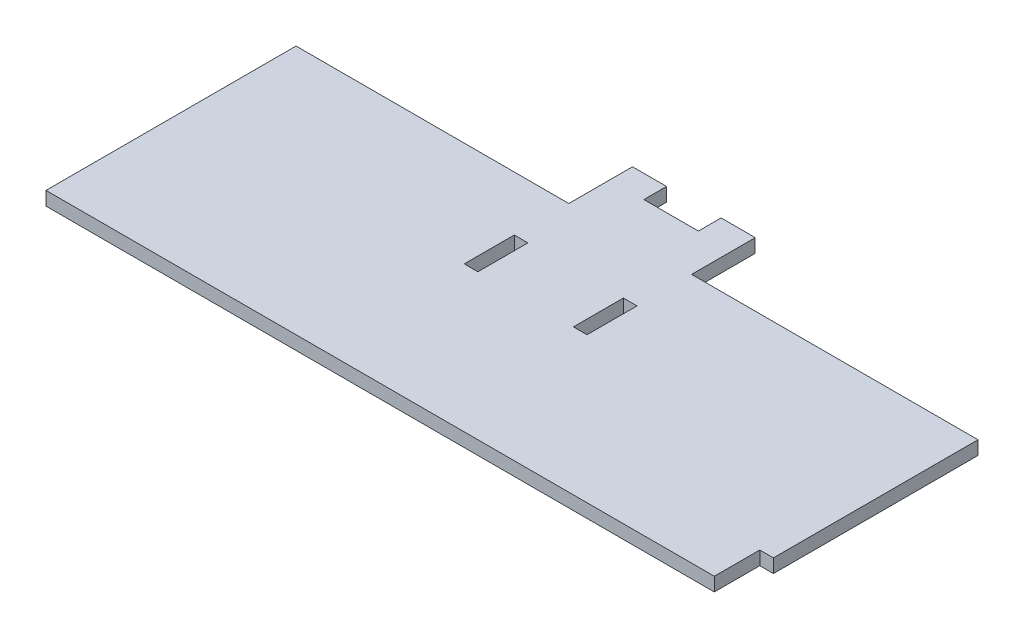
SolidWorks part; units mm, degrees
ref_plane "Front Plane" through (0, 0, 0) normal (0, 0, 1) x (1, 0, 0)
ref_plane "Top Plane" through (0, 0, 0) normal (0, 1, 0) x (1, 0, 0)
ref_plane "Right Plane" through (0, 0, 0) normal (1, 0, 0) x (0, 0, -1)
sketch "Sketch1" plane through (0, 0, 0) normal (0, 1, 0) x (1, 0, 0)
  line L0 (-107.2297, 61.3116) -> (-107.2297, 51.3116) construction
  line L1 (-104.2297, 61.3116) -> (-107.2297, 61.3116) construction
  line L2 (-107.2297, 61.3116) -> (-107.2297, 51.3116)
  line L3 (-104.2297, 61.3116) -> (-107.2297, 61.3116)
  line L5 (-107.2297, 61.3116) -> (42.7703, 61.3116)
  line L6 (-107.2297, 61.3116) -> (-107.2297, 6.3116)
  line L7 (-107.2297, 6.3116) -> (42.7703, 6.3116)
  line L8 (42.7703, 6.3116) -> (42.7703, 16.3116)
  line L9 (42.7703, 16.3116) -> (39.7703, 16.3116)
  line L10 (39.7703, 16.3116) -> (39.7703, 6.3116)
  line L11 (39.7703, 6.3116) -> (42.7703, 6.3116)
  line L12 (42.7703, 6.3116) -> (42.7703, 16.3116)
  line L13 (42.7703, 16.3116) -> (39.7703, 16.3116)
  line L14 (39.7703, 16.3116) -> (39.7703, 6.3116)
  line L15 (39.7703, 6.3116) -> (42.7703, 6.3116)
  line L16 (42.7703, 61.3116) -> (42.7703, 6.3116)
  dimension "D1" = 0
extrude "Boss-Extrude1" add sketch "Sketch1" along normal blind 3 contours L16 L5 L3 L2 L6 L7 L14 L13
sketch "Sketch2" plane through (0, 3, 0) normal (0, 1, 0) x (1, 0, 0)
  line L0 (-44.2297, 38.3116) -> (-44.2297, 48.3116) construction
  line L1 (-44.2297, 38.3116) -> (-47.2297, 38.3116) construction
  line L2 (-47.2297, 48.3116) -> (-47.2297, 38.3116) construction
  line L3 (-44.2297, 48.3116) -> (-47.2297, 48.3116) construction
  line L4 (-20.2297, 38.3116) -> (-23.2297, 38.3116) construction
  line L5 (-20.2297, 38.3116) -> (-20.2297, 48.3116) construction
  line L6 (-23.2297, 48.3116) -> (-23.2297, 38.3116) construction
  line L7 (-20.2297, 48.3116) -> (-23.2297, 48.3116) construction
  line L8 (-44.2297, 38.3116) -> (-44.2297, 48.3116)
  line L9 (-44.2297, 38.3116) -> (-47.2297, 38.3116)
  line L10 (-47.2297, 48.3116) -> (-47.2297, 38.3116)
  line L11 (-44.2297, 48.3116) -> (-47.2297, 48.3116)
  line L12 (-20.2297, 38.3116) -> (-23.2297, 38.3116)
  line L13 (-20.2297, 38.3116) -> (-20.2297, 48.3116)
  line L14 (-23.2297, 48.3116) -> (-23.2297, 38.3116)
  line L15 (-20.2297, 48.3116) -> (-23.2297, 48.3116)
  line L16 (7.7703, 42.3116) -> (-72.2297, 42.3116) construction
  line L17 (7.7703, 45.3116) -> (-72.2297, 45.3116) construction
  line L18 (7.7703, 42.3116) -> (-72.2297, 42.3116)
  line L19 (7.7703, 45.3116) -> (-72.2297, 45.3116)
  line L21 (-44.2297, 38.3116) -> (-47.2297, 38.3116)
  line L22 (-44.2297, 38.3116) -> (-44.2297, 49.3116)
  line L23 (-44.2297, 49.3116) -> (-47.2297, 49.3116)
  line L24 (-47.2297, 38.3116) -> (-47.2297, 49.3116)
  line L25 (-20.2297, 38.3116) -> (-23.2297, 38.3116)
  line L26 (-20.2297, 38.3116) -> (-20.2297, 49.3116)
  line L27 (-20.2297, 49.3116) -> (-23.2297, 49.3116)
  line L28 (-23.2297, 38.3116) -> (-23.2297, 49.3116)
  dimension "D1" = 11
  dimension "D2" = 3
  dimension "D3" = 11
  dimension "D4" = 3
extrude "Cut-Extrude2" cut sketch "Sketch2" against normal blind 3 contours L8 L18 L10 L9 | L8 L19 L10 L18 | L19 L8 L11 L10 | L24 L11 L22 L23 | L28 L15 L26 L27
sketch "Sketch3" plane through (0, 3, 0) normal (0, 1, 0) x (1, 0, 0)
  line L0 (-44.2297, 70.3109) -> (-47.2297, 70.3109) construction
  line L1 (-20.2297, 70.3109) -> (-23.2297, 70.3109) construction
  line L2 (-44.2297, 70.3109) -> (-47.2297, 70.3109)
  line L3 (-20.2297, 70.3109) -> (-23.2297, 70.3109)
  line L4 (-107.2297, 61.3116) -> (42.7703, 61.3116) construction
  line L5 (-47.2297, 61.3116) -> (-20.2297, 61.3116)
  line L6 (-47.2297, 61.3116) -> (-47.2297, 75.3116)
  line L7 (-47.2297, 75.3116) -> (-20.2297, 75.3116)
  line L8 (-20.2297, 61.3116) -> (-20.2297, 75.3116)
  dimension "D1" = 14
  dimension "D2" = 27
  dimension "D3" = 27
extrude "Boss-Extrude3" add sketch "Sketch3" against normal up to surface (3 mm away) up to face at (-8.2297, 0, -27.9783)
sketch "Sketch4" plane through (0, 3, 0) normal (0, 1, 0) x (1, 0, 0)
  line L0 (-47.2297, 75.3116) -> (-20.2297, 75.3116) construction
  line L1 (-27.7297, 80.3116) -> (-39.7297, 80.3116)
  line L2 (-27.7297, 80.3116) -> (-27.7297, 70.3116)
  line L3 (-27.7297, 70.3116) -> (-39.7297, 70.3116)
  line L4 (-39.7297, 80.3116) -> (-39.7297, 70.3116)
  line L5 (-27.7297, 80.3116) -> (-39.7297, 70.3116) construction
  line L6 (-27.7297, 70.3116) -> (-39.7297, 80.3116) construction
  point P0 (-33.7297, 75.3116)
  dimension "D1" = 12
  dimension "D2" = 10
extrude "Cut-Extrude3" cut sketch "Sketch4" against normal up to surface (3 mm away) up to face at (-24.5797, 0, -45.5116)
